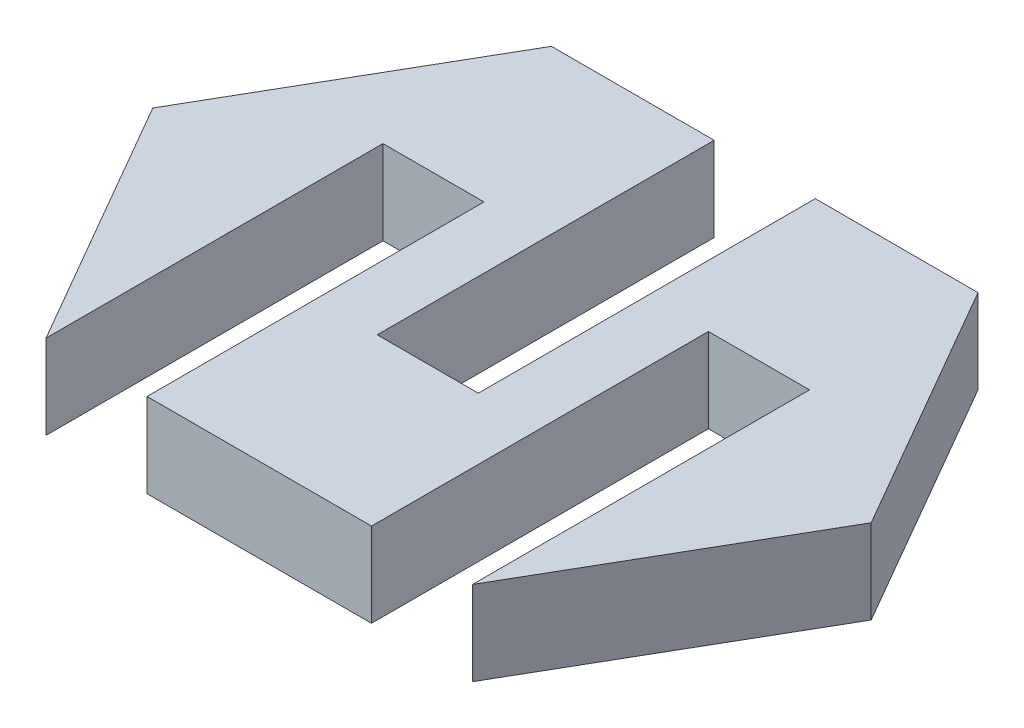
SolidWorks part; units mm, degrees
ref_plane "Front Plane" through (0, 0, 0) normal (0, 0, 1) x (1, 0, 0)
ref_plane "Top Plane" through (0, 0, 0) normal (0, 1, 0) x (1, 0, 0)
ref_plane "Right Plane" through (0, 0, 0) normal (1, 0, 0) x (0, 0, -1)
sketch "Sketch1" plane through (0, 0, 0) normal (0, 1, 0) x (1, 0, 0)
  line L0 (8.5813, -0.0094) -> (4.2512, 7.4906)
  line L7 (-8.4091, 7.4906) -> (-12.7392, -0.0094)
  line L8 (-12.7392, -0.0094) -> (-8.4091, -7.5094)
  line L9 (4.2512, -7.5094) -> (8.5813, -0.0094)
  line L10 (-8.4091, -7.5094) -> (4.2512, -7.5094)
  line L11 (4.2512, 7.4906) -> (-8.4091, 7.4906)
extrude "Boss-Extrude1" add sketch "Sketch1" along normal blind 2.5
sketch "Sketch5" plane through (0, 0, 7.5094) normal (0, 0, 1) x (1, 0, 0)
  line L0 (-8.4091, 2.5) -> (4.2512, 2.5) construction
  line L1 (-8.4091, 0) -> (-5.4091, 0)
  line L2 (-8.4091, 0) -> (-8.4091, 2.5)
  line L3 (-8.4091, 2.5) -> (-5.4091, 2.5)
  line L4 (-5.4091, 0) -> (-5.4091, 2.5)
  dimension "D1" = 3
extrude "Cut-Extrude2" cut sketch "Sketch5" against normal blind 10
sketch "Sketch6" plane through (0, 0, 7.5094) normal (0, 0, 1) x (1, 0, 0)
  line L0 (-5.4091, 2.5) -> (4.2512, 2.5) construction
  line L1 (4.2512, 0) -> (1.2512, 0)
  line L2 (4.2512, 0) -> (4.2512, 2.5)
  line L3 (4.2512, 2.5) -> (1.2512, 2.5)
  line L4 (1.2512, 0) -> (1.2512, 2.5)
  dimension "D1" = 3
extrude "Cut-Extrude3" cut sketch "Sketch6" against normal blind 10
sketch "Sketch7" plane through (0, 0, -7.4906) normal (0, 0, -1) x (-1, 0, 0)
  line L0 (-4.2512, 2.5) -> (8.4091, 2.5) construction
  line L1 (0.5788, 2.5) -> (3.5788, 2.5)
  line L2 (0.5788, 2.5) -> (0.5788, 0)
  line L3 (0.5788, 0) -> (3.5788, 0)
  line L4 (3.5788, 2.5) -> (3.5788, 0)
  line L5 (-4.2512, 0) -> (8.4091, 0) construction
  line L6 (-4.2512, 2.5) -> (-4.2512, 0) construction
  dimension "D1" = 4.83
  dimension "D2" = 3
extrude "Cut-Extrude4" cut sketch "Sketch7" against normal blind 10
